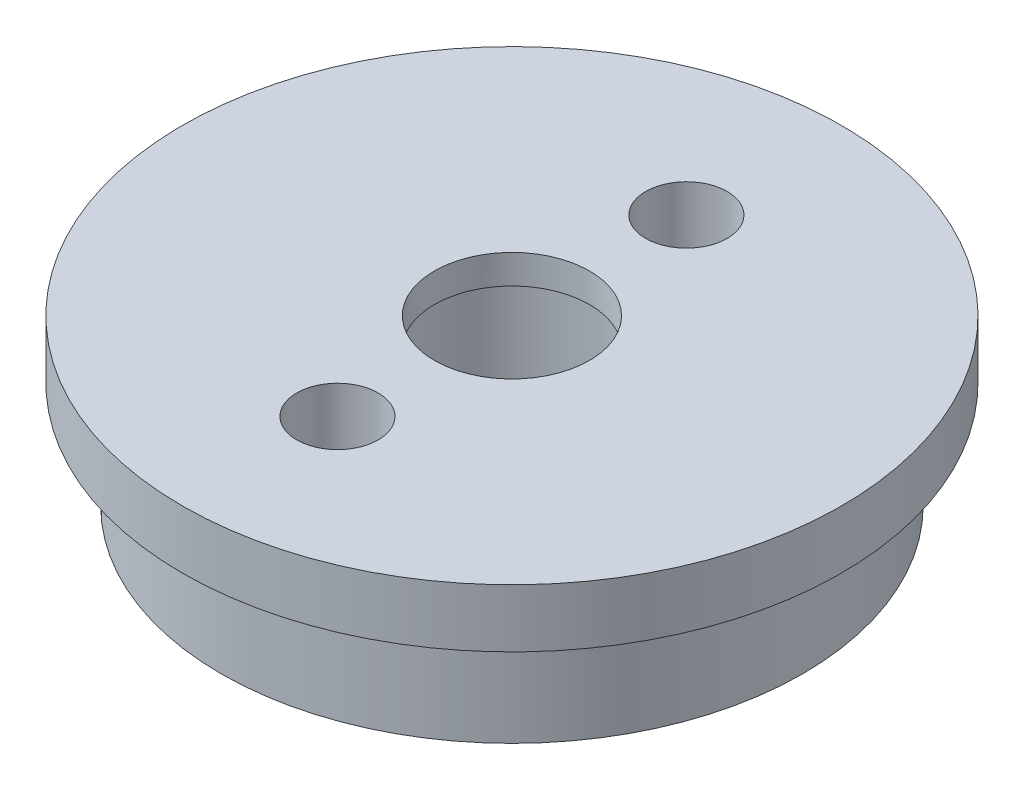
SolidWorks part; units mm, degrees
ref_plane "Front Plane" through (0, 0, 0) normal (0, 0, 1) x (1, 0, 0)
ref_plane "Top Plane" through (0, 0, 0) normal (0, 1, 0) x (1, 0, 0)
ref_plane "Right Plane" through (0, 0, 0) normal (1, 0, 0) x (0, 0, -1)
sketch "Sketch1" plane through (0, 0, 0) normal (0, 1, 0) x (1, 0, 0)
  circle A0 centre (0, 0) radius 15
  dimension "D1" = 30
extrude "Boss-Extrude1" add sketch "Sketch1" along normal blind 5.5
sketch "Sketch2" plane through (0, 5.5, 0) normal (0, 1, 0) x (1, 0, 0)
  circle A0 centre (0, 0) radius 17
  dimension "D1" = 34
extrude "Boss-Extrude2" add sketch "Sketch2" along normal blind 3
sketch "Sketch3" plane through (0, 0, 0) normal (0, -1, 0) x (1, 0, 0)
  circle A0 centre (0, 0) radius 5.1
  dimension "D1" = 10.2
extrude "Cut-Extrude1" cut sketch "Sketch3" against normal blind 7
sketch "Sketch4" plane through (0, 8.5, 0) normal (0, 1, 0) x (1, 0, 0)
  line L0 (0, 9) -> (0, -9) construction
  circle A0 centre (0, 9) radius 2.1
  circle A1 centre (0, -9) radius 2.1
  circle A2 centre (0, 0) radius 4
  point P4 (0, 0)
  dimension "D2" = 4.2
  dimension "D3" = 8
  dimension "D1" = 18
extrude "Cut-Extrude2" cut sketch "Sketch4" against normal blind 6
